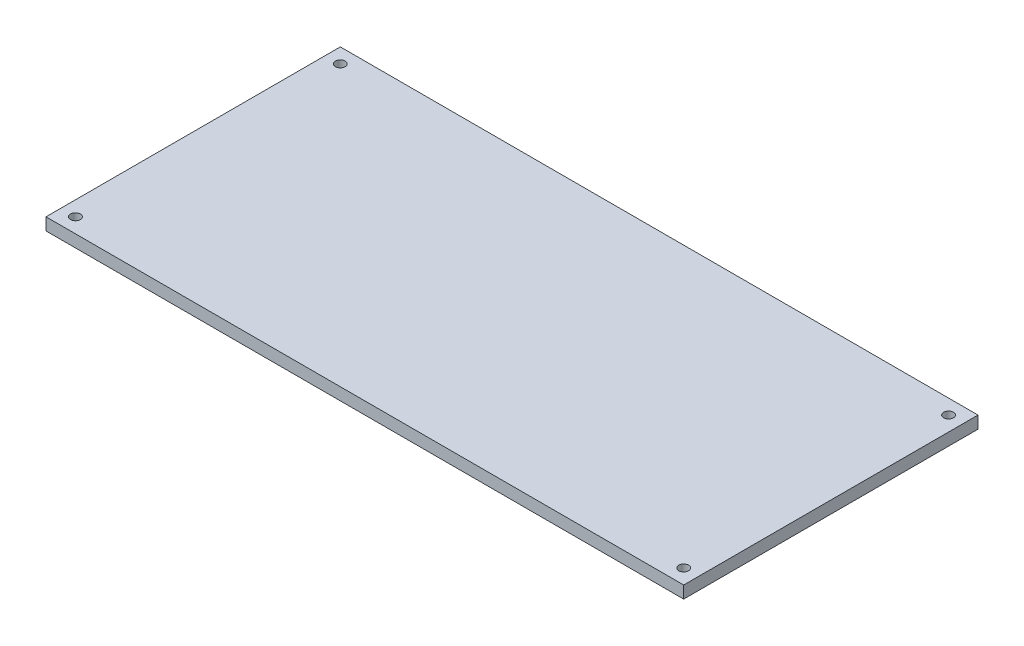
SolidWorks part; units mm, degrees
ref_plane "Front Plane" through (0, 0, 0) normal (0, 0, 1) x (1, 0, 0)
ref_plane "Top Plane" through (0, 0, 0) normal (0, 1, 0) x (1, 0, 0)
ref_plane "Right Plane" through (0, 0, 0) normal (1, 0, 0) x (0, 0, -1)
sketch "Sketch3" plane through (0, 0, 0) normal (0, 1, 0) x (1, 0, 0)
  line L1 (-65, 30) -> (65, 30)
  line L2 (-65, 30) -> (-65, -30)
  line L3 (-65, -30) -> (65, -30)
  line L4 (65, 30) -> (65, -30)
  line L5 (-65, 30) -> (65, -30) construction
  line L6 (-65, -30) -> (65, 30) construction
  point P0 (0, 0)
  dimension "D1" = 130
  dimension "D2" = 60
extrude "Boss-Extrude1" add sketch "Sketch3" along normal blind 2.5
sketch "Sketch4" plane through (0, 2.5, 0) normal (0, 1, 0) x (1, 0, 0)
  line L0 (65, 30) -> (-65, 30) construction
  line L1 (-65, 30) -> (-65, -30) construction
  line L2 (65, 30) -> (-65, 30) construction
  line L3 (65, -30) -> (65, 30) construction
  line L4 (-65, -30) -> (65, -30) construction
  line L5 (-65, 30) -> (-65, -30) construction
  circle A0 centre (-62, 27) radius 1
  circle A1 centre (62, 27) radius 1
  circle A2 centre (62, -27) radius 1
  circle A3 centre (-62, -27) radius 1
  point P10 (0, 0)
  point P14 (0, 0)
  dimension "D1" = 2
  dimension "D2" = 3
  dimension "D3" = 3
  dimension "D4" = 3
  dimension "D5" = 3
  dimension "D6" = 3
  dimension "D7" = 3
  dimension "D8" = 3
  dimension "D9" = 3
extrude "Cut-Extrude1" cut sketch "Sketch4" against normal up to next
